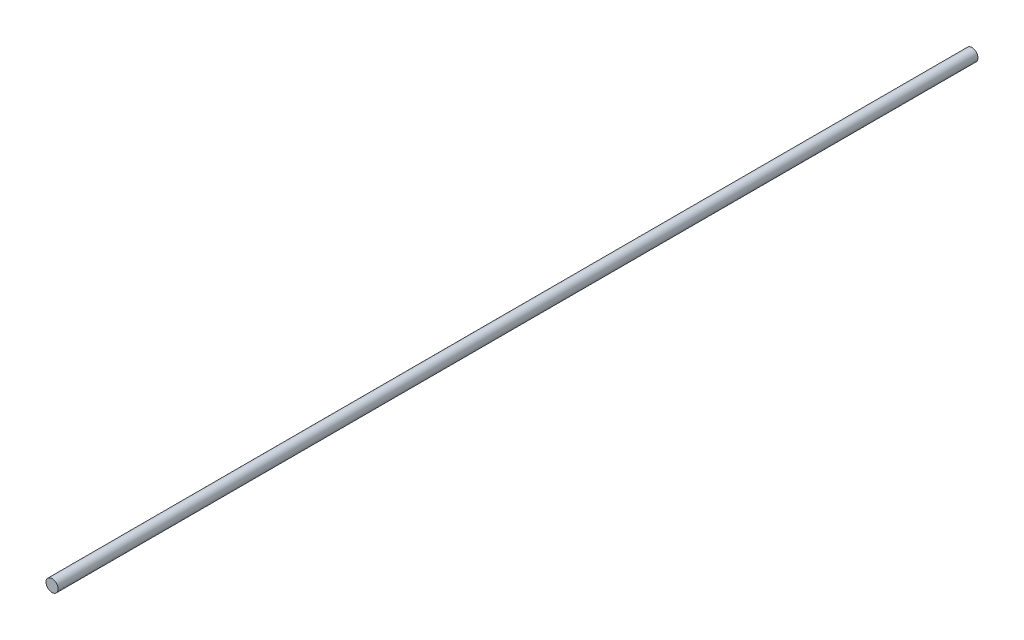
SolidWorks part; units mm, degrees
ref_plane "Front Plane" through (0, 0, 0) normal (0, 0, 1) x (1, 0, 0)
ref_plane "Top Plane" through (0, 0, 0) normal (0, 1, 0) x (1, 0, 0)
ref_plane "Right Plane" through (0, 0, 0) normal (1, 0, 0) x (0, 0, -1)
sketch "Sketch1" plane through (0, 0, 0) normal (0, 0, 1) x (1, 0, 0)
  circle A0 centre (0, 0) radius 4
extrude "Boss-Extrude1" add sketch "Sketch1" along normal blind 609.6
